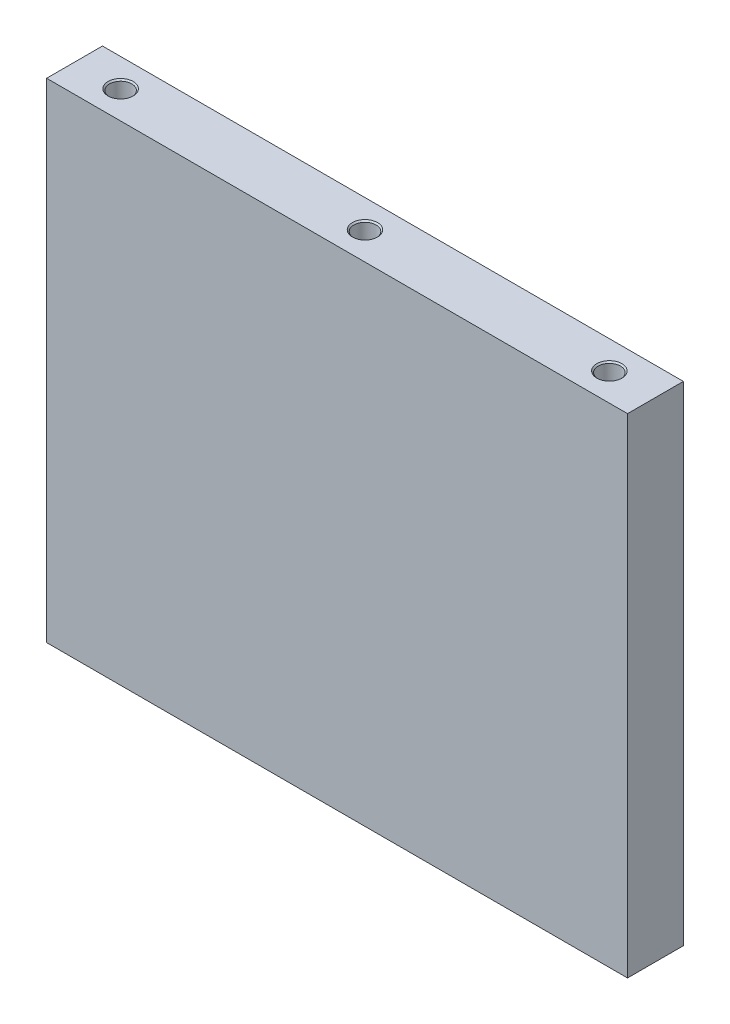
SolidWorks part; units mm, degrees
material "201 Annealed Stainless Steel (SS)"
ref_plane "Front Plane" through (0, 0, 0) normal (0, 0, 1) x (1, 0, 0)
ref_plane "Top Plane" through (0, 0, 0) normal (0, 1, 0) x (1, 0, 0)
ref_plane "Right Plane" through (0, 0, 0) normal (1, 0, 0) x (0, 0, -1)
sketch "Sketch1" plane through (0, 0, -58) normal (0, 1, 0) x (1, 0, 0)
  line L1 (-104, -68) -> (104, -68)
  line L2 (-104, -68) -> (-104, -48)
  line L3 (-104, -48) -> (104, -48)
  line L4 (104, -68) -> (104, -48)
  line L5 (0, -69) -> (0, -47) construction
  line L6 (-96.25, -58) -> (96.25, -58) construction
  point P5 (0, -68)
  point P8 (-104, -58)
  dimension "D1" = 208
  dimension "D2" = 20
extrude "Boss-Extrude1" add sketch "Sketch1" along normal blind 175
sketch "Sketch2" plane through (0, 175, 0) normal (0, 1, 0) x (1, 0, 0)
  line L0 (0, 0) -> (0, -51.17) construction
  circle A0 centre (0, 0) radius 4
  circle A1 centre (-87.5, 0) radius 4
  circle A2 centre (87.5, 0) radius 4
  dimension "D1" = 8
  dimension "D2" = 175
  dimension "D3" = 167
extrude "Cut-Extrude1" cut sketch "Sketch2" against normal blind 12
ref_plane "Plane1" through (0, 87.5, 0) normal (0, 1, 0) x (1, 0, 0)
mirror "Mirror6" about plane through (0, 87.5, 0) normal (0, 1, 0) of "Cut-Extrude1"
chamfer "Chamfer1" distance 0.5 angle 45 6 edges at (87.5, 175, -4) (0, 175, 4) (-87.5, 175, 4) (-87.5, 0, 4) (0, 0, 4) (87.5, 0, -4)
